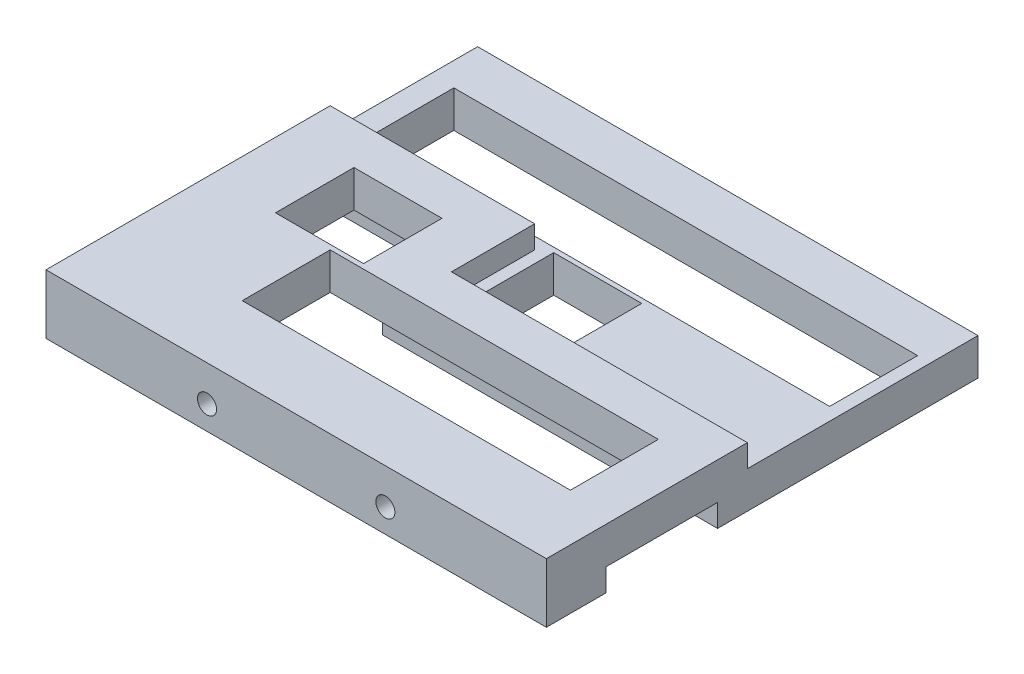
SolidWorks part; units mm, degrees
ref_plane "Front Plane" through (0, 0, 0) normal (0, 0, 1) x (1, 0, 0)
ref_plane "Top Plane" through (0, 0, 0) normal (0, 1, 0) x (1, 0, 0)
ref_plane "Right Plane" through (0, 0, 0) normal (1, 0, 0) x (0, 0, -1)
sketch "Sketch1" plane through (0, 0, 0) normal (0, 1, 0) x (1, 0, 0)
  line L0 (0, 38) -> (0, 78) construction
  line L1 (-47.7, -38) -> (47.7, -38) construction
  line L2 (-47.7, -38) -> (-47.7, 38) construction
  line L3 (-47.7, 38) -> (47.7, 38) construction
  line L4 (47.7, -38) -> (47.7, 38) construction
  line L5 (-47.7, -38) -> (47.7, 38) construction
  line L6 (-47.7, 38) -> (47.7, -38) construction
  line L7 (-52.7, 108) -> (85.3, 108)
  line L8 (-52.7, 108) -> (-52.7, 145)
  line L9 (-52.7, 145) -> (85.3, 145)
  line L10 (85.3, 108) -> (85.3, 145)
  line L11 (-77.7, 147) -> (-40.7, 147)
  line L12 (-77.7, 147) -> (-77.7, 180)
  line L13 (-77.7, 180) -> (-40.7, 180)
  line L14 (-40.7, 147) -> (-40.7, 180)
  line L15 (-14.2, 167.5) -> (22.8, 167.5)
  line L16 (-14.2, 167.5) -> (-14.2, 200.5)
  line L17 (-14.2, 200.5) -> (22.8, 200.5)
  line L18 (22.8, 167.5) -> (22.8, 200.5)
  line L19 (-95.2, 202.5) -> (99.8, 202.5)
  line L20 (-95.2, 202.5) -> (-95.2, 239.5)
  line L21 (-95.2, 239.5) -> (99.8, 239.5)
  line L22 (99.8, 202.5) -> (99.8, 239.5)
  line L27 (-105.2, 259.5) -> (105.2, 259.5)
  line L28 (-105.2, 259.5) -> (-105.2, 78)
  line L29 (-105.2, 78) -> (105.2, 78)
  line L30 (105.2, 259.5) -> (105.2, 78)
  point P0 (0, 0)
  dimension "D1" = 95.4
  dimension "D2" = 76
  dimension "D3" = 70
  dimension "D4" = 37
  dimension "D5" = 33
  dimension "D6" = 195
  dimension "D7" = 2
  dimension "D8" = 22.5
  dimension "D9" = 30
  dimension "D10" = 2
  dimension "D11" = 138
  dimension "D13" = 5
  dimension "D14" = 12
  dimension "D15" = 26.5
  dimension "D16" = 81
  dimension "D17" = 20
  dimension "D18" = 10
extrude "Boss-Extrude1" add sketch "Sketch1" along normal blind 25
sketch "Sketch2" plane through (0, 25, 0) normal (0, 1, 0) x (1, 0, 0)
  line L0 (-105.2, 197.5) -> (-19.2, 197.5)
  line L1 (-105.2, 259.5) -> (-105.2, 78) construction
  line L2 (-19.2, 197.5) -> (-19.2, 162.5)
  line L3 (-19.2, 162.5) -> (105.2, 162.5)
  line L4 (105.2, 259.5) -> (105.2, 78) construction
  line L5 (-95.2, 202.5) -> (99.8, 202.5) construction
  line L6 (-14.2, 167.5) -> (-14.2, 200.5) construction
  line L7 (-14.2, 167.5) -> (22.8, 167.5) construction
  line M4 (105.2, 78) -> (105.2, 259.5)
  line M5 (105.2, 259.5) -> (-105.2, 259.5)
  line M6 (-105.2, 259.5) -> (-105.2, 78)
  line M16 (99.8, 239.5) -> (99.8, 202.5)
  line M17 (99.8, 202.5) -> (-95.2, 202.5)
  line M18 (-95.2, 202.5) -> (-95.2, 239.5)
  line M19 (-95.2, 239.5) -> (99.8, 239.5)
  line M20 (22.8, 200.5) -> (22.8, 167.5)
  line M21 (22.8, 167.5) -> (-14.2, 167.5)
  line M22 (-14.2, 167.5) -> (-14.2, 200.5)
  line M23 (-14.2, 200.5) -> (22.8, 200.5)
  dimension "D1" = 5
  dimension "D2" = 5
  dimension "D3" = 5
extrude "Cut-Extrude1" cut sketch "Sketch2" against normal blind 9.5 and the other way through all contours L2 L3 L0 M4 M5 M6 M23 M20 M21 M22 M19 M16 M17 M18
sketch "Sketch3" plane through (0, 0, 0) normal (0, -1, 0) x (1, 0, 0)
  line L0 (-105.2, -185) -> (-35.7, -185)
  line L1 (-105.2, -259.5) -> (-105.2, -78) construction
  line L2 (-35.7, -185) -> (-35.7, -150)
  line L3 (-35.7, -150) -> (105.2, -150)
  line L4 (105.2, -259.5) -> (105.2, -78) construction
  line L5 (-77.7, -180) -> (-40.7, -180) construction
  line L6 (-40.7, -147) -> (-40.7, -180) construction
  line L7 (-52.7, -145) -> (85.3, -145) construction
  line L8 (105.2, -103) -> (-105.2, -103)
  line L9 (-105.2, -78) -> (105.2, -78) construction
  dimension "D1" = 5
  dimension "D2" = 5
  dimension "D3" = 5
  dimension "D4" = 25
extrude "Cut-Extrude2" cut sketch "Sketch3" against normal blind 9.5 and the other way through all
sketch "Sketch4" plane through (0, 0, -78) normal (0, 0, 1) x (1, 0, 0)
  line L0 (-37.5, 10) -> (37.5, 10) construction
  line L1 (0, 0) -> (0, 10) construction
  line L2 (-105.2, 0) -> (105.2, 0) construction
  dimension "D1" = 75
  dimension "D2" = 10
hole_wizard "Ø8.0mm Dowel Hole1" positions "3DSketch1" profile "Sketch5" hole size "Ø8.0" standard "ANSI Metric"
sketch3d "3DSketch1"
  point P0 (-37.5, 10, -78)
  point P3 (37.5, 10, -78)
sketch "Sketch5" plane through (-37.5, 10, -78) normal (1, 0, 0) x (0, -1, 0)
  line L0 (0, 0) -> (0, 27.4034)
  line L1 (0, 27.4034) -> (4, 25)
  line L2 (4, 25) -> (4, 0)
  line L5 (4, 0) -> (0, 0)
  line L10 (0, 27.4034) -> (-4, 25) construction
  line L11 (0, -6.35) -> (0, 107.95) construction
  dimension "Hole Dia." = 8
  dimension "Hole Depth" = 25
  dimension "Drill Angle" = 118
